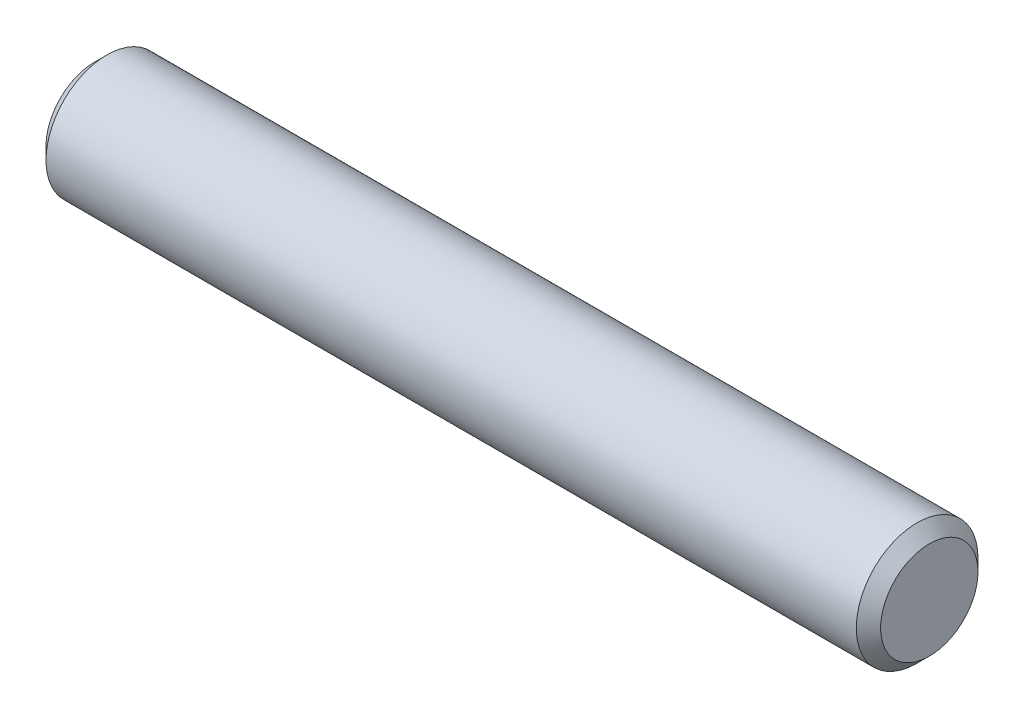
SolidWorks part; units mm, degrees
ref_plane "Front" through (0, 0, 0) normal (0, 0, 1) x (1, 0, 0)
ref_plane "Top" through (0, 0, 0) normal (0, 1, 0) x (1, 0, 0)
ref_plane "Right" through (0, 0, 0) normal (1, 0, 0) x (0, 0, -1)
sketch "Sketch1" plane through (0, 0, 0) normal (0, 0, 1) x (1, 0, 0)
  line L0 (-19.05, 0) -> (19.05, 0) construction
  line L1 (19.05, 2.7781) -> (19.05, -2.7781) construction
  line L2 (-19.05, 2.7781) -> (-19.05, -2.7781) construction
  dimension "Length" = 38.1
  dimension "Diameter" = 5.5562
sketch "Sketch2" plane through (0, 0, 0) normal (1, 0, 0) x (0, 0, -1)
  circle A0 centre (0, 0) radius 2.7781
extrude "Extrude1" add sketch "Sketch2" against normal up to vertex (19.05 mm away) and the other way up to vertex (19.05 mm away) up to point (-19.05, 2.7781, 0) other way up to point (19.05, 2.7781, 0)
chamfer "Chamfer1" distance 0.5556 angle 45 2 edges at (19.05, 0, -2.7781) (-19.05, 0, -2.7781)
equation "\"D1@Chamfer1\" = \"Diameter@Sketch1\"*.1"
